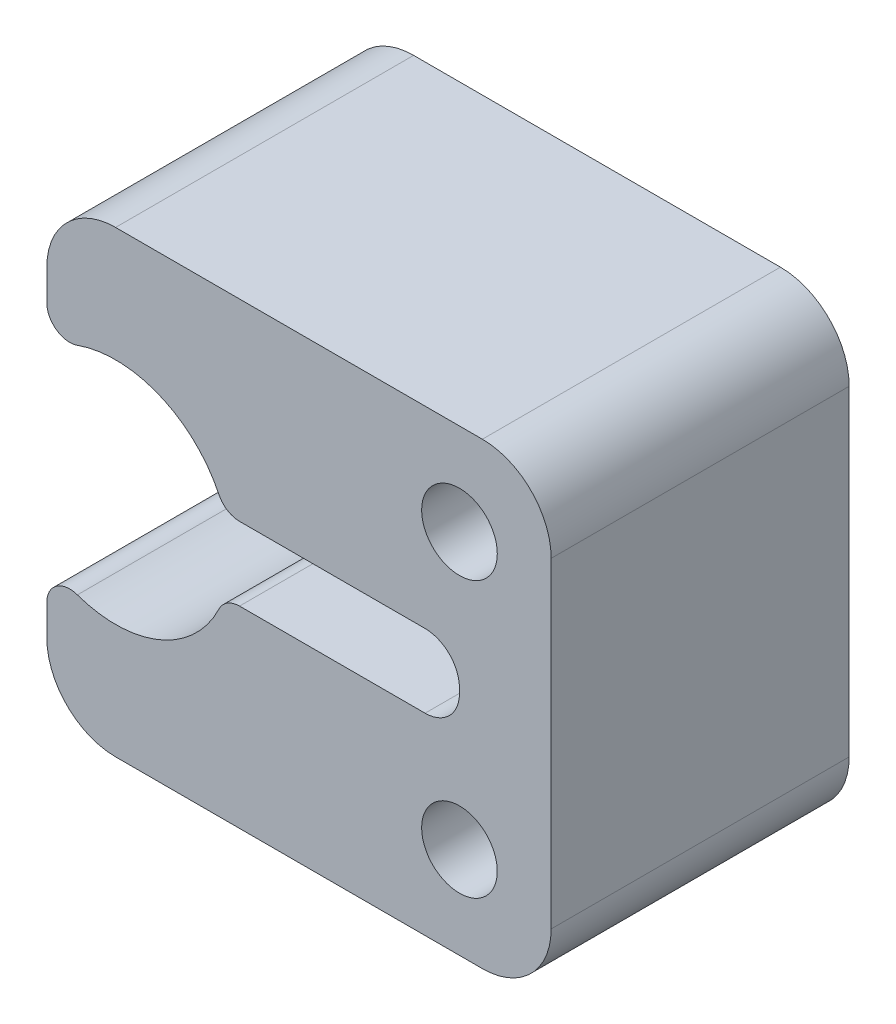
SolidWorks part; units mm, degrees
ref_plane "Plan de face" through (0, 0, 0) normal (0, 0, 1) x (1, 0, 0)
ref_plane "Plan de dessus" through (0, 0, 0) normal (0, 1, 0) x (1, 0, 0)
ref_plane "Plan de droite" through (0, 0, 0) normal (1, 0, 0) x (0, 0, -1)
sketch "Esquisse1" plane through (0, 0, 0) normal (0, 0, 1) x (1, 0, 0)
  line L1 (0, 0) -> (22, 0)
  line L2 (0, 0) -> (0, 20)
  line L3 (0, 20) -> (22, 20)
  line L4 (22, 0) -> (22, 20)
  dimension "D1" = 20
  dimension "D2" = 22
extrude "Boss.-Extru.1" add sketch "Esquisse1" along normal blind 13
sketch "Esquisse2" plane through (0, 0, 13) normal (0, 0, 1) x (1, 0, 0)
  line L0 (18, 20) -> (18, 0) construction
  line L1 (22, 20) -> (0, 20) construction
  line L2 (0, 0) -> (22, 0) construction
  line L3 (18, 10) -> (22, 10) construction
  line L4 (22, 0) -> (22, 20) construction
  line L5 (3, 0) -> (3, 20) construction
  line L6 (0, 20) -> (0, 0) construction
  line L7 (0, 6) -> (0, 14)
  circle A0 centre (18, 16) radius 1.65
  circle A1 centre (18, 4) radius 1.65
  arc A2 (0, 14) -> (0, 6) centre (3, 10) cw
  point P21 (2, 20)
  dimension "D1" = 12
  dimension "D2" = 3.3
  dimension "D3" = 5
  dimension "D4" = 3
  dimension "D5" = 15
extrude "Enlèv. mat.-Extru.1" cut sketch "Esquisse2" against normal through all both and the other way through all
sketch "Esquisse4" plane through (0, 0, 13) normal (0, 0, 1) x (1, 0, 0)
  line L0 (18, 16) -> (18, 4) construction
  line L1 (18, 10) -> (6, 10) construction
  line L2 (6, 8.4) -> (6, 11.6)
  line L3 (6, 11.6) -> (18, 11.6)
  line L4 (18, 11.6) -> (18, 8.4)
  line L5 (6, 8.4) -> (18, 8.4)
  dimension "D1" = 1.6
  dimension "D2" = 12
extrude "Enlèv. mat.-Extru.2" cut sketch "Esquisse4" against normal up to vertex (13 mm away)
fillet "Congé1" radius 1 4 edges at (0, 14, 6.5) (0, 6, 6.5) (7.7371, 8.4, 6.5) (7.7371, 11.6, 6.5)
fillet "Congé2" radius 3 4 edges at (22, 0, 6.5) (22, 20, 6.5) (0, 20, 6.5) (0, 0, 6.5)
fillet "Congé3" radius 1.5 2 edges at (18, 11.6, 6.5) (18, 8.4, 6.5)
